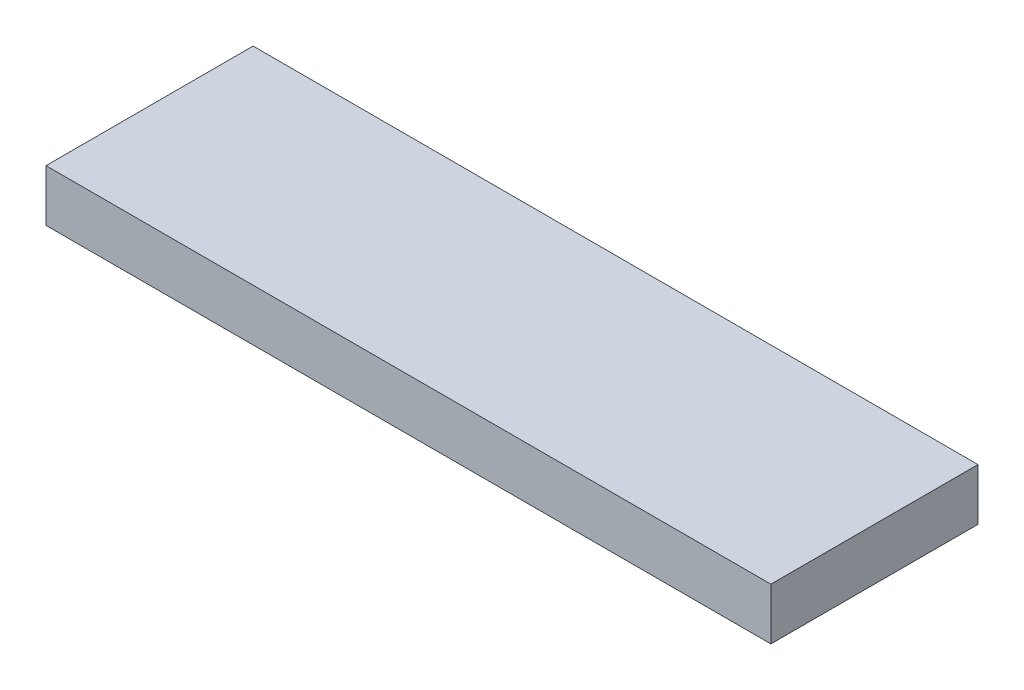
SolidWorks part; units mm, degrees
ref_plane "Front Plane" through (0, 0, 0) normal (0, 0, 1) x (1, 0, 0)
ref_plane "Top Plane" through (0, 0, 0) normal (0, 1, 0) x (1, 0, 0)
ref_plane "Right Plane" through (0, 0, 0) normal (1, 0, 0) x (0, 0, -1)
sketch "Sketch1" plane through (0, 0, 0) normal (0, 1, 0) x (1, 0, 0)
  line L0 (-17.78, -5.08) -> (17.78, 5.08) construction
  line L1 (-17.78, 5.08) -> (17.78, 5.08)
  line L2 (-17.78, 5.08) -> (-17.78, -5.08)
  line L3 (-17.78, -5.08) -> (17.78, -5.08)
  line L4 (17.78, 5.08) -> (17.78, -5.08)
  point P4 (0, 0)
  dimension "D1" = 35.56
  dimension "D2" = 10.16
extrude "Extrude1" add sketch "Sketch1" along normal blind 2.54
